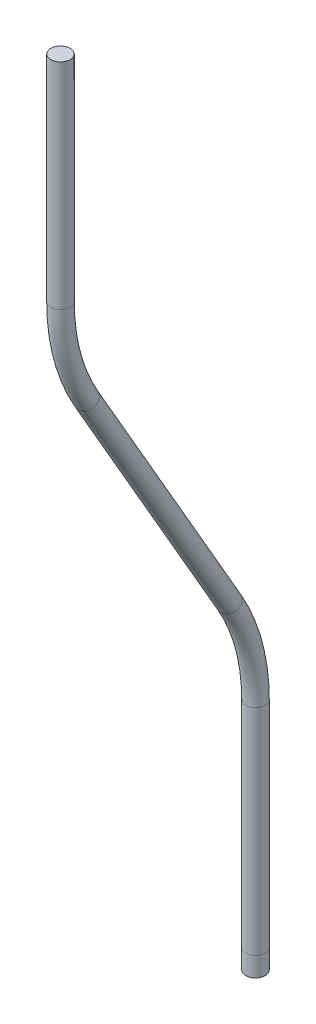
SolidWorks part; units mm, degrees
ref_plane "Front Plane" through (0, 0, 0) normal (0, 0, 1) x (1, 0, 0)
ref_plane "Top Plane" through (0, 0, 0) normal (0, 1, 0) x (1, 0, 0)
ref_plane "Right Plane" through (0, 0, 0) normal (1, 0, 0) x (0, 0, -1)
sketch "Sketch2" plane through (0, 0, 0) normal (1, 0, 0) x (0, 0, -1)
  line L3 (-20, 91.359) -> (-20, 69.359)
  line L4 (-17.3205, 59.359) -> (-2.6795, 34)
  line L5 (0, 24) -> (0, 2)
  line L6 (0, 2) -> (0, 0)
  arc A2 (-20, 69.359) -> (-17.3205, 59.359) centre (0, 69.359) ccw
  arc A3 (0, 24) -> (-2.6795, 34) centre (-20, 24) ccw
  point P3 (-243.7228, 170.4479)
  point P9 (0, 187.2141)
  point P10 (-15.4252, 130.0226)
  point P13 (0, 0)
  point P14 (0, 0)
  point P15 (0, 0)
  point P16 (0, 0)
  dimension "D3" = 20
  dimension "D6" = 20
  dimension "D1" = 20
  dimension "D2" = 22
  dimension "D4" = 2
  dimension "D5" = 30
sweep "Sweep1" add path "Sketch2" circular profile diameter 2 parameters "D3"=2
